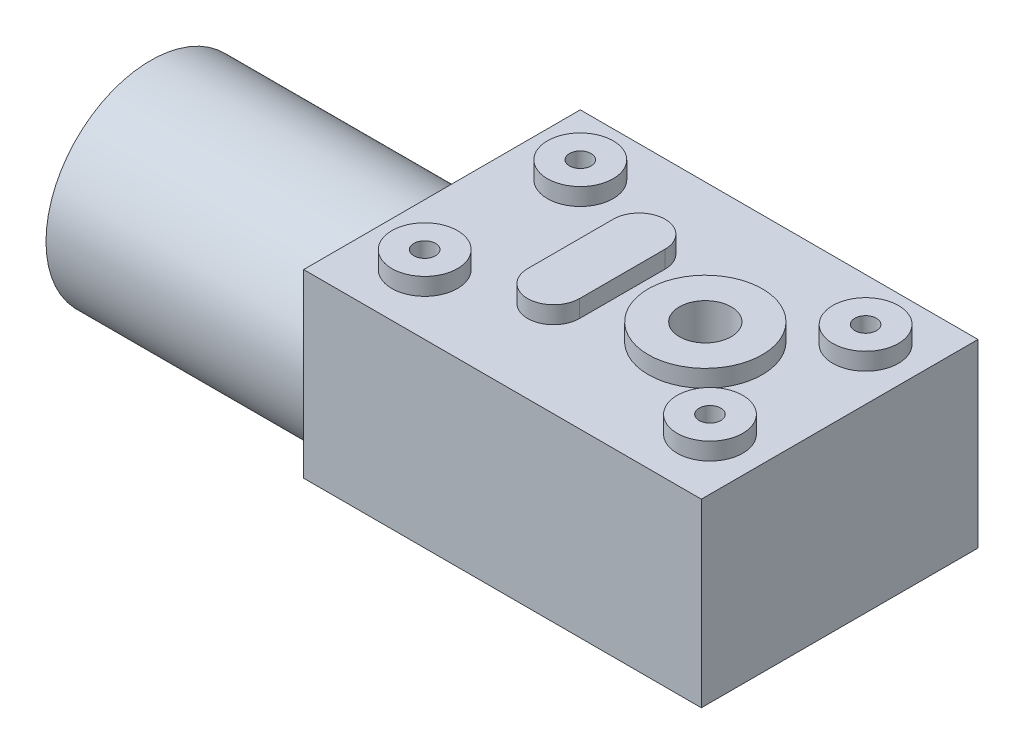
SolidWorks part; units mm, degrees
material "Zinc AG40A (Zn-4Al-0.4Mg; Zamak 3), Cast"
ref_plane "Front Plane" through (0, 0, 0) normal (0, 0, 1) x (1, 0, 0)
ref_plane "Top Plane" through (0, 0, 0) normal (0, 1, 0) x (1, 0, 0)
ref_plane "Right Plane" through (0, 0, 0) normal (1, 0, 0) x (0, 0, -1)
sketch "Sketch1" plane through (0, 0, 0) normal (0, 1, 0) x (1, 0, 0)
  line L1 (-23, -16) -> (23, -16)
  line L2 (-23, -16) -> (-23, 16)
  line L3 (-23, 16) -> (23, 16)
  line L4 (23, -16) -> (23, 16)
  line L5 (-23, -16) -> (23, 16) construction
  line L6 (-23, 16) -> (23, -16) construction
  line L7 (-16.5394, 9.0215) -> (16.4606, 9.0215)
  line L8 (-16.5394, 9.0215) -> (-16.5394, -8.9785)
  line L9 (-16.5394, -8.9785) -> (16.4606, -8.9785)
  line L10 (16.4606, 9.0215) -> (16.4606, -8.9785)
  circle A0 centre (7.4606, 0) radius 3
  point P1 (0, 0)
  dimension "D3" = 33
  dimension "D8" = 6
  dimension "D1" = 32
  dimension "D2" = 46
  dimension "D4" = 18
  dimension "D5" = 9
extrude "Boss-Extrude1" add sketch "Sketch1" along normal blind 22.3
sketch "Sketch3" plane through (0, 22.3, 0) normal (0, 1, 0) x (1, 0, 0)
  line L0 (-23, -16) -> (-23, 16) construction
  line L1 (-16, -9) -> (17, -9) construction
  line L2 (-16, -9) -> (-16, 9) construction
  line L3 (-16, 9) -> (17, 9) construction
  line L4 (17, -9) -> (17, 9) construction
  line L5 (-23, 16) -> (23, 16) construction
  line L6 (-5.1394, -4.95) -> (-5.1394, 4.95) construction
  line L7 (-8.1394, -4.95) -> (-8.1394, 4.95)
  line L8 (-2.1394, -4.95) -> (-2.1394, 4.95)
  line L9 (23, 0) -> (-23, 0) construction
  line L10 (23, -16) -> (23, 16) construction
  line L11 (-2.1394, 0) -> (0.8606, 0) construction
  line L12 (-16, -9) -> (17, -9) construction
  circle A0 centre (-16, -9) radius 3.8
  circle A4 centre (7.4606, 0) radius 6.6
  arc A5 (-8.1394, -4.95) -> (-2.1394, -4.95) centre (-5.1394, -4.95) ccw
  arc A6 (-2.1394, 4.95) -> (-8.1394, 4.95) centre (-5.1394, 4.95) ccw
  circle A7 centre (17, -9) radius 3.8
  circle A8 centre (17, 9) radius 3.8
  circle A9 centre (-16, 9) radius 3.8
  point P17 (-5.1394, 0)
  dimension "D5" = 7.6
  dimension "D6" = 13.2
  dimension "D1" = 33
  dimension "D2" = 18
  dimension "D3" = 7
  dimension "D4" = 7
  dimension "D7" = 6
  dimension "D8" = 9.9
  dimension "D9" = 3
  dimension "D12" = 33
  dimension "D10" = 2
  dimension "D11" = 2
extrude "Boss-Extrude3" add sketch "Sketch3" along normal blind 2
sketch "Sketch2" plane through (-23, 0, 0) normal (-1, 0, 0) x (0, 0, 1)
  line L0 (2.9, 21.3) -> (2.9, 22.3) construction
  line L1 (16, 22.3) -> (-16, 22.3) construction
  line L2 (15, 9.2) -> (16, 9.2) construction
  line L3 (16, 22.3) -> (16, 0) construction
  circle A0 centre (2.9, 9.2) radius 12.1
  dimension "D1" = 24.2
  dimension "D2" = 1
  dimension "D3" = 1
sketch "Sketch4" plane through (0, 22.3, 0) normal (0, -1, 0) x (1, 0, 0)
  circle A0 centre (7.4606, 0) radius 3 construction
  circle A1 centre (7.4606, 0) radius 3
extrude "Cut-Extrude1" cut sketch "Sketch4" against normal through all
extrude "Boss-Extrude2" add sketch "Sketch2" along normal blind 30.8
chamfer "Chamfer1" distance 1.4 angle 75 3 edges at (0, 0, 16) (23, 0, 0) (0, 0, -16)
hole_wizard "Tap Drill for M3x0.5 Tap1" positions "Sketch5" profile "Sketch6" hole size "M3x0.5" standard "ANSI Metric"
sketch "Sketch5" plane through (0, 24.3, 0) normal (0, 1, 0) x (1, 0, 0)
  point P0 (-16, -9)
  point P17 (-16, 9)
  point P20 (17, 9)
  point P23 (17, -9)
  point P26 (17, -9)
sketch "Sketch6" plane through (-16, 24.3, 9) normal (1, 0, 0) x (0, 0, 1)
  line L0 (0, 0) -> (0, 3.3511)
  line L1 (0, 3.3511) -> (1.25, 2.6)
  line L2 (1.25, 2.6) -> (1.25, 0)
  line L5 (1.25, 0) -> (0, 0)
  line L10 (0, 3.3511) -> (-1.25, 2.6) construction
  line L11 (0, -6.35) -> (0, 107.95) construction
  dimension "Hole Dia." = 2.5
  dimension "Hole Depth" = 2.6
  dimension "Drill Angle" = 118
sketch "Sketch8" plane through (-53.8, 0, 0) normal (-1, 0, 0) x (0, 0, 1)
  circle A3 centre (2.9, 9.2) radius 11.8
  circle A4 centre (2.9, 9.2) radius 11.8
  dimension "D1" = 0.3
extrude "Cut-Extrude2" cut sketch "Sketch8" against normal blind 0.8
sketch "Sketch7" plane through (-53, 0, 0) normal (-1, 0, 0) x (0, 0, 1)
  circle A0 centre (2.9, 9.2) radius 3.2
  dimension "D1" = 6.4
extrude "Boss-Extrude5" add sketch "Sketch7" along normal blind 2.7
